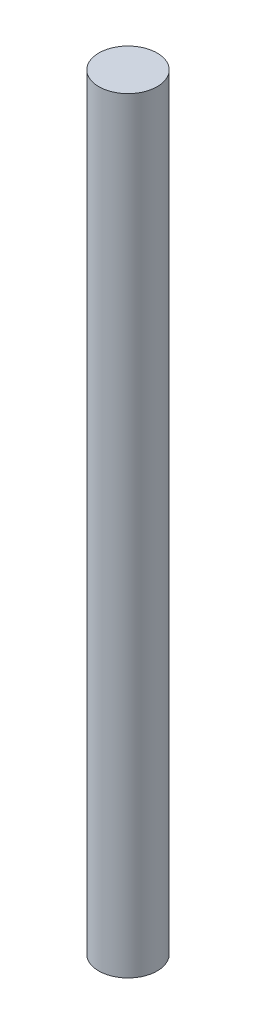
SolidWorks part; units mm, degrees
ref_plane "前视基准面" through (0, 0, 0) normal (0, 0, 1) x (1, 0, 0)
ref_plane "上视基准面" through (0, 0, 0) normal (0, 1, 0) x (1, 0, 0)
ref_plane "右视基准面" through (0, 0, 0) normal (1, 0, 0) x (0, 0, -1)
ref_plane "基准面4" through (0, 0, 0) normal (0, 0, -1) x (-1, 0, 0)
sketch "草图1" plane through (0, 0, 0) normal (0, 0, -1) x (-1, 0, 0)
  line L0 (-144, -105) -> (-140, -105)
  line L1 (-140, -105) -> (-140, 0)
  line L2 (-140, 0) -> (-144, 0)
  line L3 (-144, 0) -> (-144, -105)
  line L4 (-140, -105) -> (-140, 0) construction
revolve "旋转1" add sketch "草图1" angle 360 about L4
